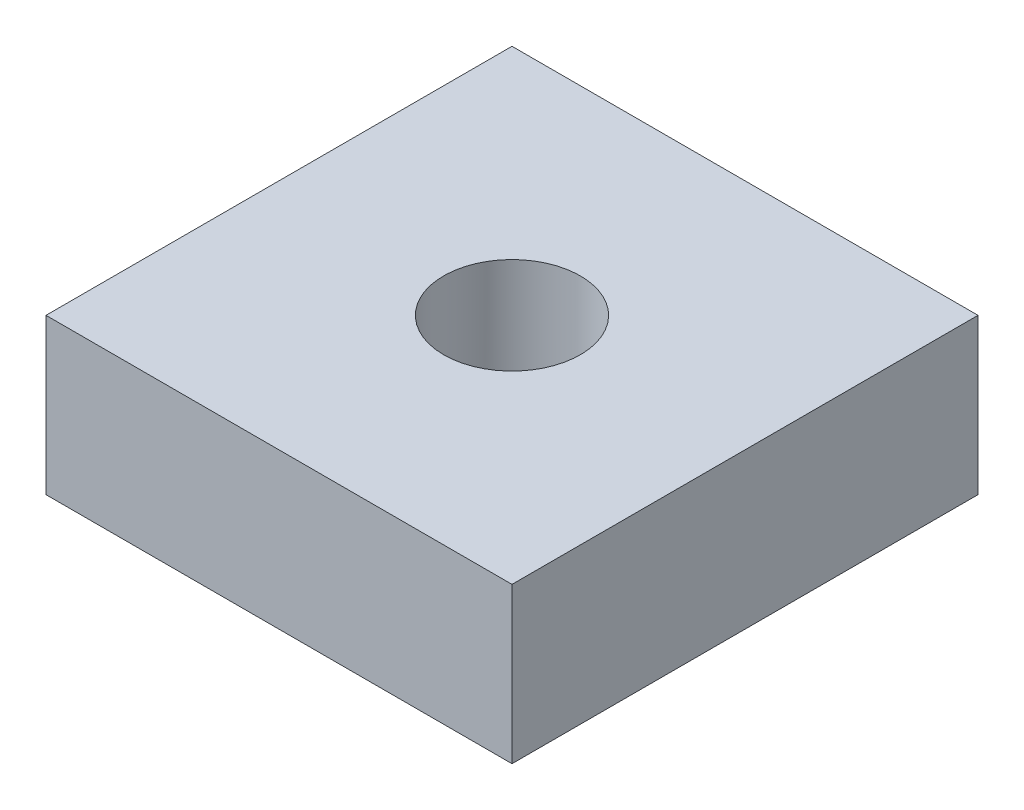
SolidWorks part; units mm, degrees
ref_plane "Front Plane" through (0, 0, 0) normal (0, 0, 1) x (1, 0, 0)
ref_plane "Top Plane" through (0, 0, 0) normal (0, 1, 0) x (1, 0, 0)
ref_plane "Right Plane" through (0, 0, 0) normal (1, 0, 0) x (0, 0, -1)
sketch "Sketch1" plane through (0, 0, 0) normal (0, 1, 0) x (1, 0, 0)
  line L1 (-19.05, -19.05) -> (19.05, -19.05)
  line L2 (-19.05, -19.05) -> (-19.05, 19.05)
  line L3 (-19.05, 19.05) -> (19.05, 19.05)
  line L4 (19.05, -19.05) -> (19.05, 19.05)
  line L5 (-19.05, -19.05) -> (19.05, 19.05) construction
  line L6 (-19.05, 19.05) -> (19.05, -19.05) construction
  point P0 (0, 0)
  dimension "D1" = 38.1
extrude "Boss-Extrude1" add sketch "Sketch1" along normal blind 12.7
sketch "Sketch2" plane through (0, 12.7, 0) normal (0, 1, 0) x (1, 0, 0)
  circle A0 centre (0, 0) radius 5.588
  dimension "D1" = 11.176
extrude "Cut-Extrude1" cut sketch "Sketch2" against normal up to next
